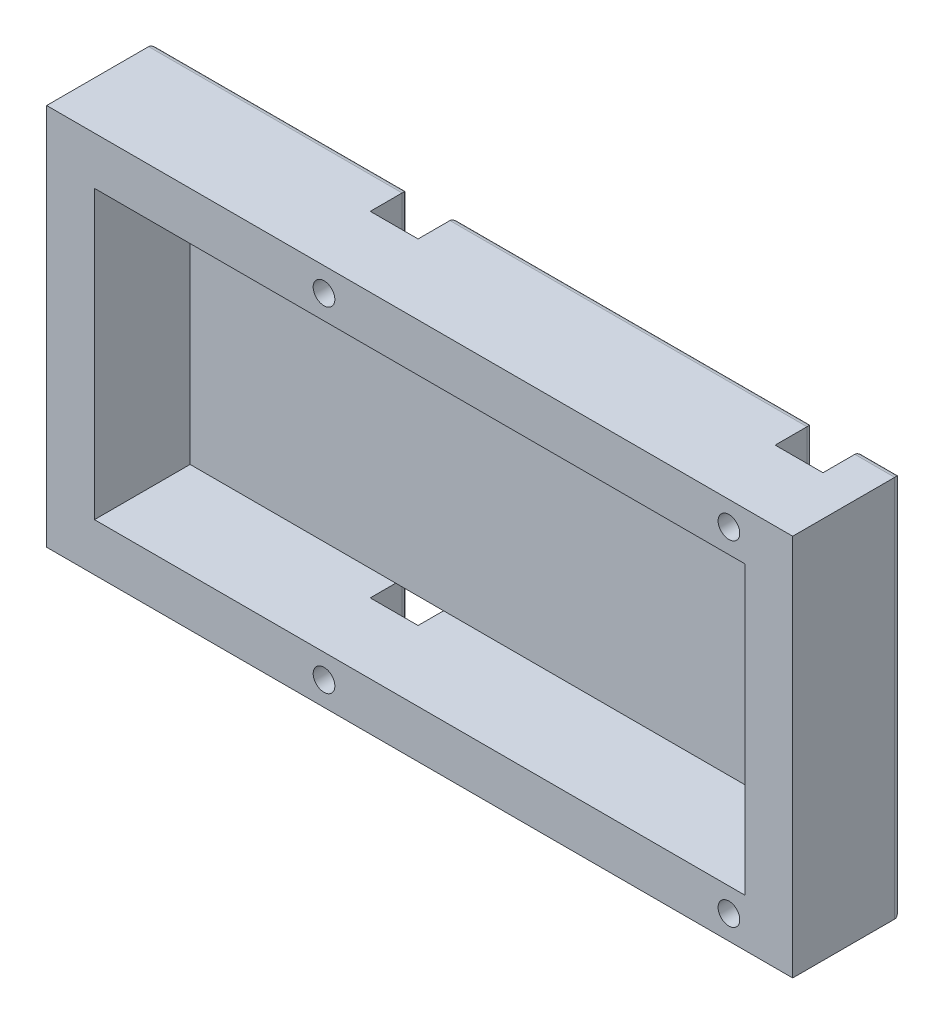
SolidWorks part; units mm, degrees
material "ABS"
ref_plane "Front" through (0, 0, 0) normal (0, 0, 1) x (1, 0, 0)
ref_plane "Top" through (0, 0, 0) normal (0, 1, 0) x (1, 0, 0)
ref_plane "Right" through (0, 0, 0) normal (1, 0, 0) x (0, 0, -1)
sketch "ｽｹｯﾁ1" plane through (0, 0, 0) normal (0, 0, 1) x (1, 0, 0)
  line L1 (58.5, 30) -> (-58.5, 30)
  line L2 (58.5, 30) -> (58.5, -30)
  line L3 (58.5, -30) -> (-58.5, -30)
  line L4 (-58.5, 30) -> (-58.5, -30)
  line L5 (58.5, 30) -> (-58.5, -30) construction
  line L6 (58.5, -30) -> (-58.5, 30) construction
  point P0 (0, 0)
  dimension "D1" = 117
  dimension "D2" = 60
extrude "ﾎﾞｽ - 押し出し1" add sketch "ｽｹｯﾁ1" along normal blind 17
sketch "ｽｹｯﾁ2" plane through (0, 0, 17) normal (0, 0, 1) x (1, 0, 0)
  line L0 (58.5, 30) -> (-58.5, 30) construction
  line L1 (51, 22.5) -> (-51, 22.5)
  line L2 (51, 22.5) -> (51, -22.5)
  line L3 (51, -22.5) -> (-51, -22.5)
  line L4 (-51, 22.5) -> (-51, -22.5)
  line L5 (51, 22.5) -> (-51, -22.5) construction
  line L6 (51, -22.5) -> (-51, 22.5) construction
  point P0 (0, 0)
  dimension "D1" = 102
  dimension "D2" = 7.5
extrude "ｶｯﾄ - 押し出し1" cut sketch "ｽｹｯﾁ2" against normal offset from surface (15 mm away) 2 up to face at (0, 0, 0)
sketch "ｽｹｯﾁ4" plane through (0, 0, 0) normal (0, 0, -1) x (-1, 0, 0)
  line L0 (-58.5, -30) -> (-58.5, 30) construction
  line L1 (-58.5, 30) -> (58.5, 30) construction
  line L2 (58.5, -30) -> (-58.5, -30) construction
  circle A0 centre (15, 26.25) radius 1.7
  circle A1 centre (15, -26.25) radius 1.7
  circle A2 centre (-48.5, -26.25) radius 1.7
  circle A3 centre (-48.5, 26.25) radius 1.7
  dimension "D1" = 3.4
  dimension "D2" = 10
  dimension "D3" = 3.75
  dimension "D4" = 3.75
  dimension "D5" = 73.5
extrude "ｶｯﾄ - 押し出し2" cut sketch "ｽｹｯﾁ4" against normal through all
sketch "ｽｹｯﾁ5" plane through (0, 0, 0) normal (0, 0, -1) x (-1, 0, 0)
  line L0 (58.5, -30) -> (-58.5, -30) construction
  line L1 (-52.25, -22.5) -> (-44.75, -22.5)
  line L2 (-52.25, -22.5) -> (-52.25, -30)
  line L3 (-52.25, -30) -> (-44.75, -30)
  line L4 (-44.75, -22.5) -> (-44.75, -30)
  line L5 (-52.25, -22.5) -> (-44.75, -30) construction
  line L6 (-52.25, -30) -> (-44.75, -22.5) construction
  line L7 (-58.5, 30) -> (58.5, 30) construction
  line L8 (-52.25, 30) -> (-44.75, 30)
  line L9 (-52.25, 30) -> (-52.25, 22.5)
  line L10 (-52.25, 22.5) -> (-44.75, 22.5)
  line L11 (-44.75, 30) -> (-44.75, 22.5)
  line L12 (-52.25, 30) -> (-44.75, 22.5) construction
  line L13 (-52.25, 22.5) -> (-44.75, 30) construction
  line L14 (11.25, 30) -> (18.75, 30)
  line L15 (11.25, 30) -> (11.25, 22.5)
  line L16 (11.25, 22.5) -> (18.75, 22.5)
  line L17 (18.75, 30) -> (18.75, 22.5)
  line L18 (11.25, 30) -> (18.75, 22.5) construction
  line L19 (11.25, 22.5) -> (18.75, 30) construction
  line L20 (11.25, -22.5) -> (18.75, -22.5)
  line L21 (11.25, -22.5) -> (11.25, -30)
  line L22 (11.25, -30) -> (18.75, -30)
  line L23 (18.75, -22.5) -> (18.75, -30)
  line L24 (11.25, -22.5) -> (18.75, -30) construction
  line L25 (11.25, -30) -> (18.75, -22.5) construction
  point P0 (-48.5, -26.25)
  point P8 (-48.5, 26.25)
  point P14 (15, 26.25)
  point P20 (15, -26.25)
extrude "ｶｯﾄ - 押し出し3" cut sketch "ｽｹｯﾁ5" against normal blind 6
fillet "ﾌｨﾚｯﾄ2" radius 1 20 edges at (44.75, 26.25, 0) (48.5, 22.5, 0) (55.375, 30, 0) (52.25, 26.25, 0) (16.75, 30, 0) (-11.25, 26.25, 0) (-15, 22.5, 0) (-18.75, 26.25, 0) (-38.625, 30, 0) (-58.5, 0, 0) (-38.625, -30, 0) (-18.75, -26.25, 0) (-15, -22.5, 0) (-11.25, -26.25, 0) (52.25, -26.25, 0) (48.5, -22.5, 0) (44.75, -26.25, 0) (16.75, -30, 0) (55.375, -30, 0) (58.5, 0, 0)
